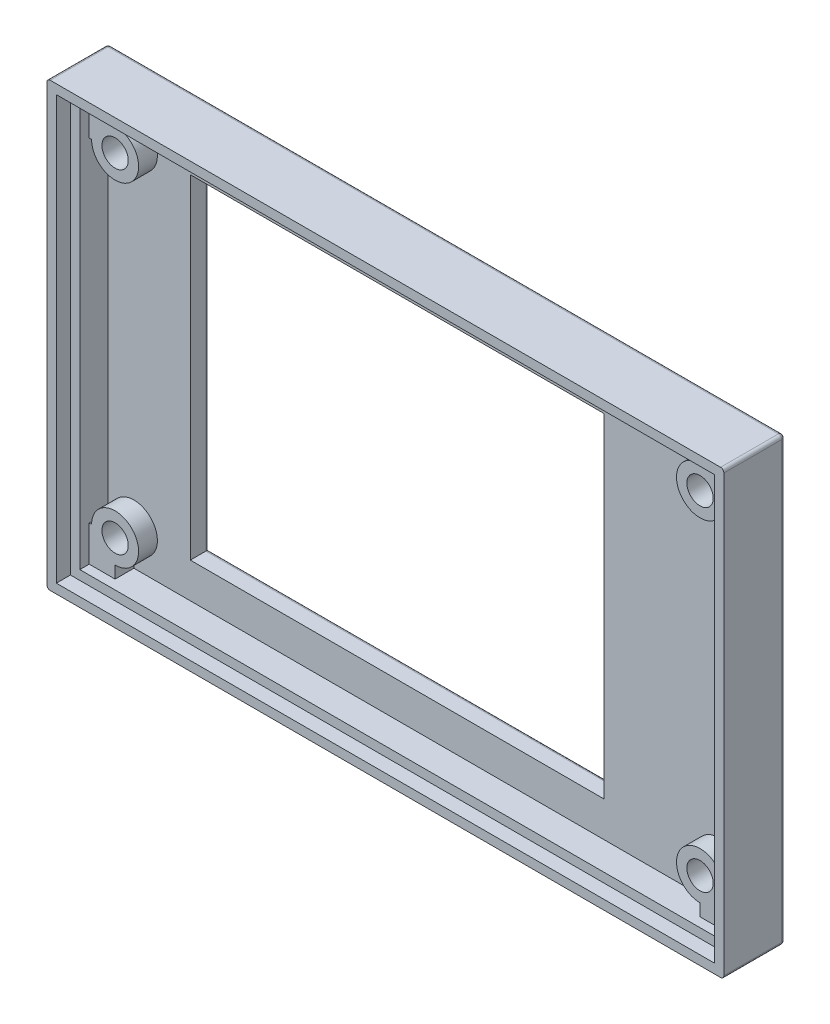
SolidWorks part; units mm, degrees
material "ABS"
ref_plane "Front Plane" through (0, 0, 0) normal (0, 0, 1) x (1, 0, 0)
ref_plane "Top Plane" through (0, 0, 0) normal (0, 1, 0) x (1, 0, 0)
ref_plane "Right Plane" through (0, 0, 0) normal (1, 0, 0) x (0, 0, -1)
sketch "Sketch1" plane through (0, 0, 0) normal (0, 0, 1) x (1, 0, 0)
  line L1 (36, -23.5) -> (-36, -23.5)
  line L2 (36, -23.5) -> (36, 23.5)
  line L3 (36, 23.5) -> (-36, 23.5)
  line L4 (-36, -23.5) -> (-36, 23.5)
  line L5 (36, -23.5) -> (-36, 23.5) construction
  line L6 (36, 23.5) -> (-36, -23.5) construction
  point P0 (0, 0)
  dimension "D1" = 72
  dimension "D2" = 47
extrude "Boss-Extrude1" add sketch "Sketch1" along normal blind 6.5
shell "Shell1" thickness 2
sketch "Sketch2" plane through (0, 0, 0) normal (0, 0, -1) x (-1, 0, 0)
  line L1 (-18.75, 17.75) -> (25.25, 17.75)
  line L2 (-18.75, 17.75) -> (-18.75, -17.75)
  line L3 (-18.75, -17.75) -> (25.25, -17.75)
  line L4 (25.25, 17.75) -> (25.25, -17.75)
  line L5 (36, 23.5) -> (36, -23.5) construction
  dimension "D1" = 35.5
  dimension "D2" = 44
  dimension "D3" = 17.75
  dimension "D4" = 10.75
extrude "Cut-Extrude1" cut sketch "Sketch2" against normal through all
sketch "Sketch3" plane through (0, 0, 2) normal (0, 0, 1) x (1, 0, 0)
  line L0 (-34, 21.5) -> (-34, -21.5) construction
  line L1 (34, 21.5) -> (-34, 21.5) construction
  circle A0 centre (-31.25, 17.75) radius 2.5
  circle A1 centre (30.96, 17.75) radius 2.5
  circle A2 centre (-31.25, -17.71) radius 2.5
  circle A3 centre (30.96, -17.71) radius 2.5
  dimension "D1" = 5
  dimension "D2" = 2.75
  dimension "D3" = 3.75
  dimension "D4" = 2
  dimension "D5" = 2
extrude "Boss-Extrude2" add sketch "Sketch3" along normal blind 2
sketch "Sketch5" plane through (0, 0, 2) normal (0, 0, 1) x (1, 0, 0)
  line L1 (-34, -21.5) -> (-31.25, -21.5)
  line L2 (-34, -21.5) -> (-34, -17.71)
  line L3 (-34, -17.71) -> (-31.25, -17.71)
  line L4 (-31.25, -21.5) -> (-31.25, -17.71)
  line L5 (-34, 21.5) -> (-31.25, 21.5)
  line L6 (-34, 21.5) -> (-34, 17.75)
  line L7 (-34, 17.75) -> (-31.25, 17.75)
  line L8 (-31.25, 21.5) -> (-31.25, 17.75)
  line L9 (34, 21.5) -> (30.96, 21.5)
  line L10 (34, 21.5) -> (34, 17.75)
  line L11 (34, 17.75) -> (30.96, 17.75)
  line L12 (30.96, 21.5) -> (30.96, 17.75)
  line L13 (34, -21.5) -> (30.96, -21.5)
  line L14 (34, -21.5) -> (34, -17.71)
  line L15 (34, -17.71) -> (30.96, -17.71)
  line L16 (30.96, -21.5) -> (30.96, -17.71)
  circle A0 centre (-31.25, -17.71) radius 2.5 construction
  circle A1 centre (-31.25, 17.75) radius 2.5 construction
  dimension "D3" = 0
  dimension "D1" = 0
  dimension "D2" = 0
extrude "Boss-Extrude3" add sketch "Sketch5" along normal blind 2
sketch "Sketch6" plane through (0, 0, 4) normal (0, 0, 1) x (1, 0, 0)
  circle A0 centre (-31.25, -17.71) radius 1.4
  circle A1 centre (-31.25, 17.75) radius 1.4
  circle A2 centre (30.96, 17.75) radius 1.4
  circle A3 centre (30.96, -17.71) radius 1.4
  dimension "D1" = 2.8
  dimension "D2" = 2.8
  dimension "D3" = 2.8
  dimension "D4" = 2.8
extrude "Cut-Extrude2" cut sketch "Sketch6" against normal blind 2
sketch "Sketch7" plane through (0, 0, 6.5) normal (0, 0, 1) x (1, 0, 0)
  line L0 (36, 23.5) -> (-36, 23.5) construction
  line L1 (35, -22.5) -> (-35, -22.5)
  line L2 (35, -22.5) -> (35, 22.5)
  line L3 (35, 22.5) -> (-35, 22.5)
  line L4 (-35, -22.5) -> (-35, 22.5)
  line L5 (35, -22.5) -> (-35, 22.5) construction
  line L6 (35, 22.5) -> (-35, -22.5) construction
  line L7 (-36, 23.5) -> (-36, -23.5) construction
  point P0 (0, 0)
  dimension "D1" = 1
  dimension "D2" = 1
extrude "Cut-Extrude3" cut sketch "Sketch7" against normal blind 1.5
fillet "Fillet1" radius 0.35 12 edges at (-3.25, -17.75, 0) (-25.25, 0, 0) (18.75, 0, 0) (-3.25, 17.75, 0) (36, 23.5, 3.25) (36, -23.5, 3.25) (-36, -23.5, 3.25) (-36, 23.5, 3.25) (-36, 0, 0) (0, -23.5, 0) (36, 0, 0) (0, 23.5, 0)
